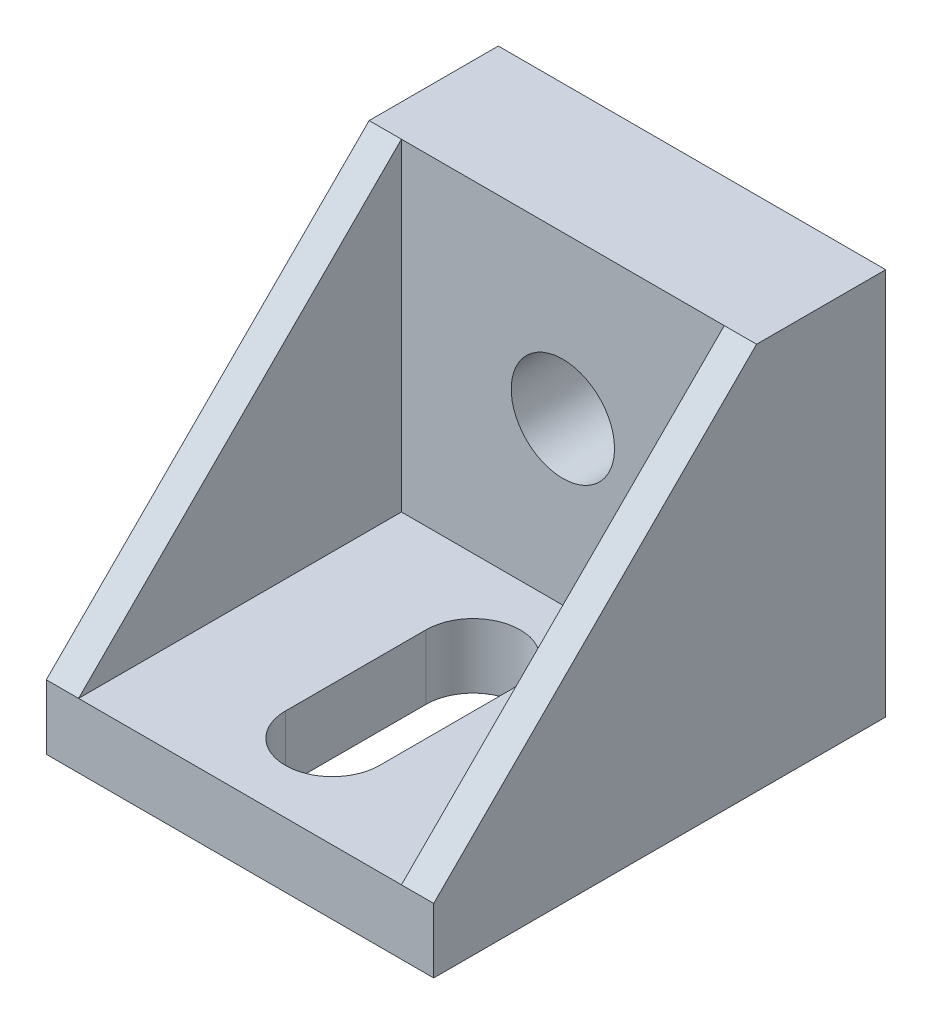
SolidWorks part; units mm, degrees
ref_plane "Front Plane" through (0, 0, 0) normal (0, 0, 1) x (1, 0, 0)
ref_plane "Top Plane" through (0, 0, 0) normal (0, 1, 0) x (1, 0, 0)
ref_plane "Right Plane" through (0, 0, 0) normal (1, 0, 0) x (0, 0, -1)
sketch "Sketch1" plane through (0, 0, 0) normal (0, 0, 1) x (1, 0, 0)
  line L1 (-15, 12.5) -> (15, 12.5)
  line L2 (-15, 12.5) -> (-15, -12.5)
  line L3 (-15, -12.5) -> (15, -12.5)
  line L4 (15, 12.5) -> (15, -12.5)
  line L5 (-15, 12.5) -> (15, -12.5) construction
  line L6 (-15, -12.5) -> (15, 12.5) construction
  circle A1 centre (0, 0) radius 4
  point P0 (0, 0)
  point P6 (0, 0)
  dimension "D3" = 8
  dimension "D1" = 30
  dimension "D2" = 25
extrude "Boss-Extrude1" add sketch "Sketch1" along normal blind 10
sketch "Sketch2" plane through (0, -12.5, 0) normal (0, -1, 0) x (1, 0, 0)
  line L1 (-15, 35) -> (15, 35)
  line L2 (-15, 35) -> (-15, 0)
  line L3 (-15, 0) -> (15, 0)
  line L4 (15, 35) -> (15, 0)
  line L5 (-15, 35) -> (15, 0) construction
  line L6 (-15, 0) -> (15, 35) construction
  point P0 (0, 17.5)
  dimension "D1" = 35
extrude "Boss-Extrude3" add sketch "Sketch2" along normal blind 5
sketch "Sketch7" plane through (15, 0, 0) normal (1, 0, 0) x (0, 0, -1)
  line L0 (-35, -12.5) -> (-10, 12.5)
  line L1 (-10, 12.5) -> (-10, -12.5)
  line L2 (-10, -12.5) -> (-10, 12.5) construction
  line L3 (-10, -12.5) -> (-35, -12.5) construction
  line L4 (-10, -12.5) -> (-35, -12.5)
extrude "Boss-Extrude4" add sketch "Sketch7" against normal blind 2.5
mirror "Mirror1" about plane through (0, 0, 0) normal (1, 0, 0) of "Boss-Extrude4"
sketch "Sketch8" plane through (0, -12.5, 0) normal (0, 1, 0) x (1, 0, 0)
  line L0 (0, -16.9481) -> (0, -27.8422) construction
  line L1 (3.6474, -16.9481) -> (3.6474, -27.8422)
  line L2 (-3.6474, -16.9481) -> (-3.6474, -27.8422)
  arc A0 (3.6474, -16.9481) -> (-3.6474, -16.9481) centre (0, -16.9481) ccw
  arc A1 (-3.6474, -27.8422) -> (3.6474, -27.8422) centre (0, -27.8422) ccw
  point P3 (0, -22.3951)
extrude "Cut-Extrude1" cut sketch "Sketch8" against normal through all both and the other way through all
